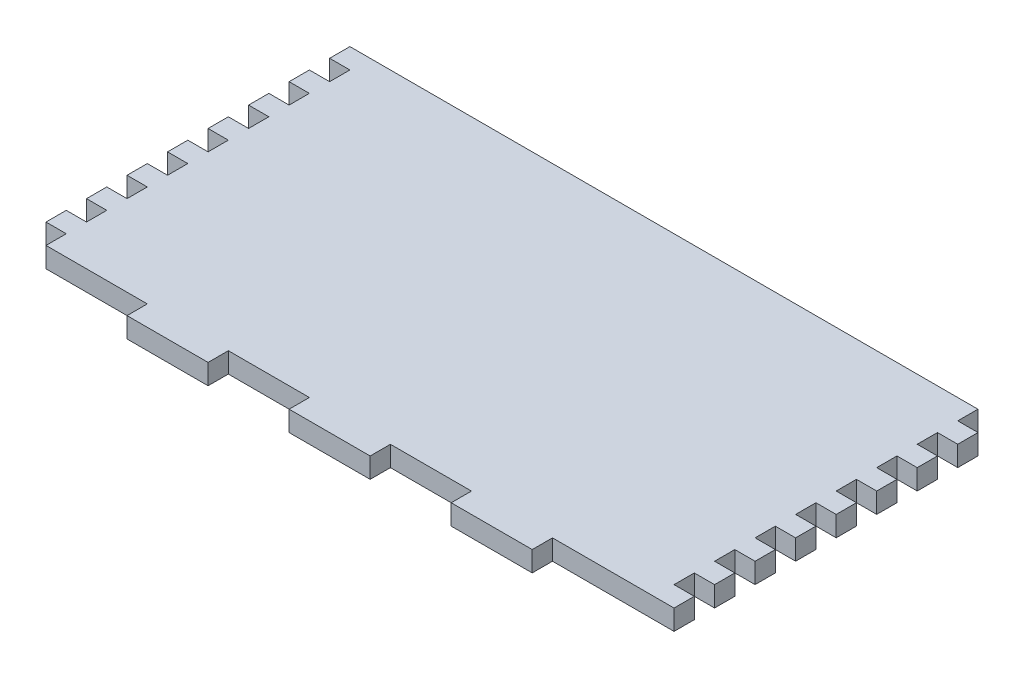
SolidWorks part; units mm, degrees
ref_plane "Front Plane" through (0, 0, 0) normal (0, 0, 1) x (1, 0, 0)
ref_plane "Top Plane" through (0, 0, 0) normal (0, 1, 0) x (1, 0, 0)
ref_plane "Right Plane" through (0, 0, 0) normal (1, 0, 0) x (0, 0, -1)
sketch "Sketch1" plane through (0, 0, 0) normal (0, 1, 0) x (1, 0, 0)
  line L1 (-84.7474, 46.7618) -> (118.4526, 46.7618)
  line L2 (-84.7474, 46.7618) -> (-84.7474, -61.1882)
  line L3 (-84.7474, -61.1882) -> (118.4526, -61.1882)
  line L4 (118.4526, 46.7618) -> (118.4526, -61.1882)
  dimension "D1" = 107.95
  dimension "D2" = 203.2
extrude "Boss-Extrude1" add sketch "Sketch1" along normal blind 6.35
sketch "Sketch2" plane through (0, 6.35, 0) normal (0, 1, 0) x (1, 0, 0)
  line L0 (-84.7474, -61.1882) -> (118.4526, -61.1882) construction
  line L1 (80.3526, -54.8382) -> (118.4526, -54.8382)
  line L2 (80.3526, -54.8382) -> (80.3526, -61.1882)
  line L3 (80.3526, -61.1882) -> (118.4526, -61.1882)
  line L4 (118.4526, -54.8382) -> (118.4526, -61.1882)
  line L5 (118.4526, -61.1882) -> (118.4526, 46.7618) construction
  line L6 (-84.7474, 46.7618) -> (-84.7474, -61.1882) construction
  line L7 (29.5526, -61.1882) -> (54.9526, -61.1882)
  line L8 (29.5526, -61.1882) -> (29.5526, -54.8382)
  line L9 (29.5526, -54.8382) -> (54.9526, -54.8382)
  line L10 (54.9526, -61.1882) -> (54.9526, -54.8382)
  line L11 (4.1526, -61.1882) -> (-21.2474, -61.1882)
  line L12 (4.1526, -61.1882) -> (4.1526, -54.8382)
  line L13 (4.1526, -54.8382) -> (-21.2474, -54.8382)
  line L14 (-21.2474, -61.1882) -> (-21.2474, -54.8382)
  line L15 (-84.7474, -61.1882) -> (-46.6474, -61.1882)
  line L16 (-84.7474, -61.1882) -> (-84.7474, -54.8382)
  line L17 (-84.7474, -54.8382) -> (-46.6474, -54.8382)
  line L18 (-46.6474, -61.1882) -> (-46.6474, -54.8382)
  dimension "D1" = 38.1
  dimension "D2" = 6.35
  dimension "D3" = 0
  dimension "D4" = 25.4
  dimension "D5" = 25.4
  dimension "D6" = 6.35
  dimension "D7" = 25.4
  dimension "D8" = 25.4
  dimension "D9" = 6.35
  dimension "D10" = 38.1
  dimension "D11" = 0
extrude "Cut-Extrude1" cut sketch "Sketch2" against normal through all
sketch "Sketch3" plane through (0, 6.35, 0) normal (0, 1, 0) x (1, 0, 0)
  line L0 (118.4526, -54.8382) -> (118.4526, 46.7618) construction
  line L1 (112.1026, -42.1382) -> (118.4526, -42.1382)
  line L2 (112.1026, -42.1382) -> (112.1026, -48.4882)
  line L3 (112.1026, -48.4882) -> (118.4526, -48.4882)
  line L4 (118.4526, -42.1382) -> (118.4526, -48.4882)
  line L5 (118.4526, -54.8382) -> (80.3526, -54.8382) construction
  line L6 (112.1026, -29.4382) -> (118.4526, -29.4382)
  line L7 (112.1026, -29.4382) -> (112.1026, -35.7882)
  line L8 (112.1026, -35.7882) -> (118.4526, -35.7882)
  line L9 (118.4526, -29.4382) -> (118.4526, -35.7882)
  line L10 (112.1026, -16.7382) -> (118.4526, -16.7382)
  line L11 (112.1026, -16.7382) -> (112.1026, -23.0882)
  line L12 (112.1026, -23.0882) -> (118.4526, -23.0882)
  line L13 (118.4526, -16.7382) -> (118.4526, -23.0882)
  line L14 (112.1026, -4.0193) -> (118.4526, -4.0193)
  line L15 (112.1026, -4.0193) -> (112.1026, -10.3693)
  line L16 (112.1026, -10.3693) -> (118.4526, -10.3693)
  line L17 (118.4526, -4.0193) -> (118.4526, -10.3693)
  line L18 (112.1026, 8.6807) -> (118.4526, 8.6807)
  line L19 (112.1026, 8.6807) -> (112.1026, 2.3307)
  line L20 (112.1026, 2.3307) -> (118.4526, 2.3307)
  line L21 (118.4526, 8.6807) -> (118.4526, 2.3307)
  line L22 (112.1026, 21.3807) -> (118.4526, 21.3807)
  line L23 (112.1026, 21.3807) -> (112.1026, 15.0307)
  line L24 (112.1026, 15.0307) -> (118.4526, 15.0307)
  line L25 (118.4526, 21.3807) -> (118.4526, 15.0307)
  line L26 (112.1026, 34.0807) -> (118.4526, 34.0807)
  line L27 (112.1026, 34.0807) -> (112.1026, 27.7307)
  line L28 (112.1026, 27.7307) -> (118.4526, 27.7307)
  line L29 (118.4526, 34.0807) -> (118.4526, 27.7307)
  line L30 (112.1026, 46.7807) -> (118.4526, 46.7807)
  line L31 (112.1026, 46.7807) -> (112.1026, 40.4307)
  line L32 (112.1026, 40.4307) -> (118.4526, 40.4307)
  line L33 (118.4526, 46.7807) -> (118.4526, 40.4307)
  line L34 (-84.7474, -48.4882) -> (-78.3974, -48.4882)
  line L35 (-84.7474, -48.4882) -> (-84.7474, -54.8382)
  line L36 (-84.7474, -54.8382) -> (-78.3974, -54.8382)
  line L37 (-78.3974, -48.4882) -> (-78.3974, -54.8382)
  line L38 (-46.6474, -54.8382) -> (-84.7474, -54.8382) construction
  line L39 (-84.7474, 46.7618) -> (-84.7474, -54.8382) construction
  line L40 (-84.7474, -35.7882) -> (-78.3974, -35.7882)
  line L41 (-84.7474, -35.7882) -> (-84.7474, -42.1382)
  line L42 (-84.7474, -42.1382) -> (-78.3974, -42.1382)
  line L43 (-78.3974, -35.7882) -> (-78.3974, -42.1382)
  line L44 (-84.7474, -23.0882) -> (-78.3974, -23.0882)
  line L45 (-84.7474, -23.0882) -> (-84.7474, -29.4382)
  line L46 (-84.7474, -29.4382) -> (-78.3974, -29.4382)
  line L47 (-78.3974, -23.0882) -> (-78.3974, -29.4382)
  line L48 (-84.7474, -10.3882) -> (-78.3974, -10.3882)
  line L49 (-84.7474, -10.3882) -> (-84.7474, -16.7382)
  line L50 (-84.7474, -16.7382) -> (-78.3974, -16.7382)
  line L51 (-78.3974, -10.3882) -> (-78.3974, -16.7382)
  line L52 (-84.7474, 2.3118) -> (-78.3974, 2.3118)
  line L53 (-84.7474, 2.3118) -> (-84.7474, -4.0382)
  line L54 (-84.7474, -4.0382) -> (-78.3974, -4.0382)
  line L55 (-78.3974, 2.3118) -> (-78.3974, -4.0382)
  line L56 (-84.7474, 15.0118) -> (-78.3974, 15.0118)
  line L57 (-84.7474, 15.0118) -> (-84.7474, 8.6618)
  line L58 (-84.7474, 8.6618) -> (-78.3974, 8.6618)
  line L59 (-78.3974, 15.0118) -> (-78.3974, 8.6618)
  line L60 (-84.7474, 27.7118) -> (-78.3974, 27.7118)
  line L61 (-84.7474, 27.7118) -> (-84.7474, 21.3618)
  line L62 (-84.7474, 21.3618) -> (-78.3974, 21.3618)
  line L63 (-78.3974, 27.7118) -> (-78.3974, 21.3618)
  line L64 (-84.7474, 40.4118) -> (-78.3974, 40.4118)
  line L65 (-84.7474, 40.4118) -> (-84.7474, 34.0618)
  line L66 (-84.7474, 34.0618) -> (-78.3974, 34.0618)
  line L67 (-78.3974, 40.4118) -> (-78.3974, 34.0618)
  point P6 (112.1026, -45.3132)
  point P33 (-84.7474, -26.2632)
  point P44 (118.4526, 43.6057)
  point P59 (-84.7474, -13.5632)
  point P64 (-84.7474, -0.8632)
  point P69 (-84.7474, 11.8368)
  point P74 (-84.7474, 24.5368)
  point P79 (-84.7474, 37.2368)
  dimension "D1" = 6.35
  dimension "D2" = 6.35
  dimension "D3" = 6.35
  dimension "D4" = 6.35
  dimension "D5" = 6.35
  dimension "D6" = 6.35
  dimension "D7" = 6.35
  dimension "D8" = 6.35
  dimension "D9" = 6.35
  dimension "D10" = 0
  dimension "D11" = 6.35
  dimension "D12" = 6.35
  dimension "D13" = 6.369
  dimension "D14" = 6.35
  dimension "D15" = 6.35
  dimension "D16" = 0
  dimension "D17" = 6.35
  dimension "D18" = 6.35
  dimension "D19" = 6.35
  dimension "D20" = 0
  dimension "D21" = 6.35
  dimension "D22" = 6.35
  dimension "D23" = 6.35
  dimension "D24" = 6.35
  dimension "D25" = 0
  dimension "D26" = 6.35
  dimension "D27" = 6.35
  dimension "D28" = 0
  dimension "D29" = 6.35
  dimension "D30" = 6.35
  dimension "D31" = 6.35
  dimension "D32" = 0
  dimension "D33" = 0
  dimension "D34" = 6.35
  dimension "D35" = 6.35
  dimension "D36" = 6.35
  dimension "D37" = 0
  dimension "D38" = 6.35
  dimension "D39" = 6.35
  dimension "D40" = 0
  dimension "D41" = 6.35
  dimension "D42" = 6.35
  dimension "D43" = 6.35
  dimension "D44" = 0
  dimension "D45" = 6.35
  dimension "D46" = 6.35
  dimension "D47" = 6.35
  dimension "D48" = 0
  dimension "D49" = 6.35
  dimension "D50" = 6.35
  dimension "D51" = 6.35
  dimension "D52" = 0
  dimension "D53" = 6.35
  dimension "D54" = 6.35
  dimension "D55" = 6.35
  dimension "D56" = 0
  dimension "D57" = 6.35
  dimension "D58" = 6.35
  dimension "D59" = 6.35
  dimension "D60" = 0
  dimension "D61" = 6.35
extrude "Cut-Extrude2" cut sketch "Sketch3" against normal through all
